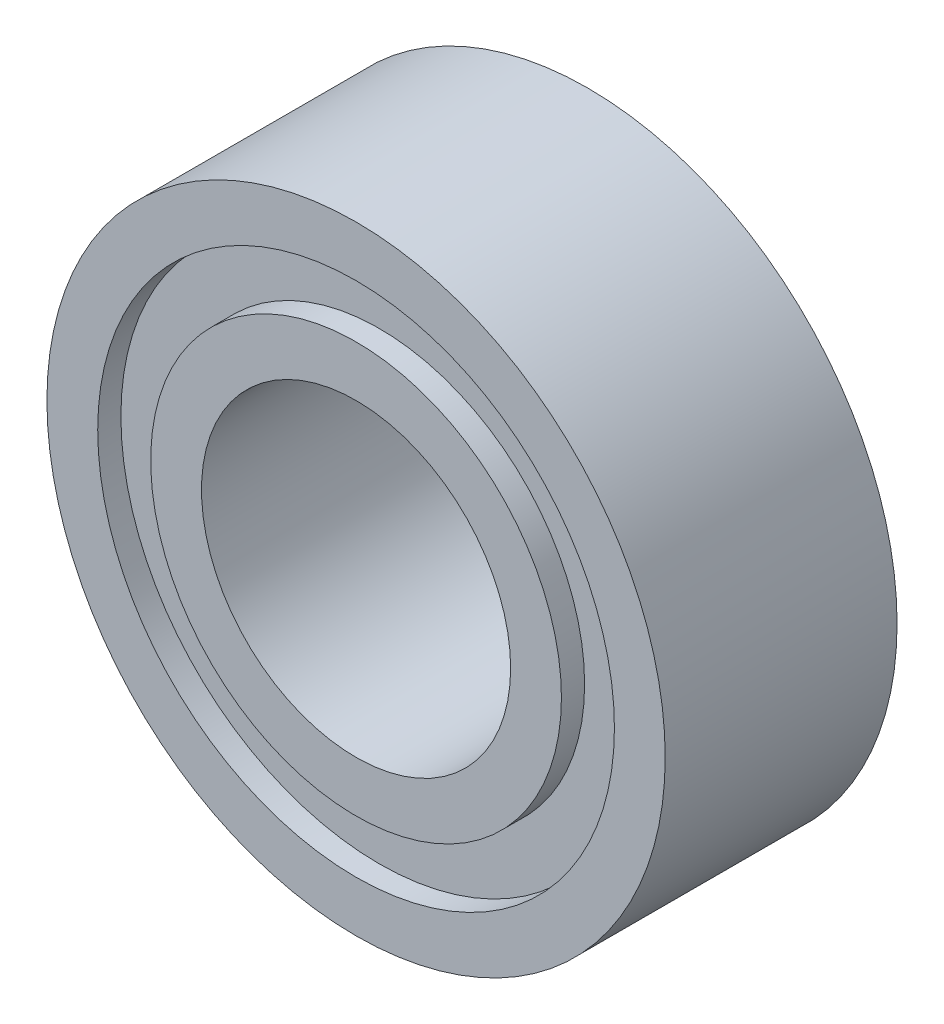
SolidWorks part; units mm, degrees
material "Легированная сталь"
ref_plane "Спереди" through (0, 0, 0) normal (0, 0, 1) x (1, 0, 0)
ref_plane "Сверху" through (0, 0, 0) normal (0, 1, 0) x (1, 0, 0)
ref_plane "Справа" through (0, 0, 0) normal (1, 0, 0) x (0, 0, -1)
sketch "Эскиз1" plane through (0, 0, 0) normal (1, 0, 0) x (0, 0, -1)
  line L0 (1.5, 2) -> (-1.5, 2)
  line L2 (-1.5, 4) -> (1.5, 4)
  line L4 (0, 0) -> (0, 50000) construction
  line L5 (-1.5, 2) -> (-1.5, 2.6571)
  line L6 (-1.5, 2.6571) -> (-1.2, 2.6571)
  line L7 (1.5, 2.6571) -> (1.5, 2)
  line L8 (-1.5, 4) -> (-1.5, 3.3429)
  line L9 (-1.5, 3.3429) -> (-1.2, 3.3429)
  line L10 (1.5, 3.3429) -> (1.5, 4)
  line L11 (0.4924, 3.3429) -> (1, 3.3429)
  line L12 (0.4924, 2.6571) -> (1, 2.6571)
  line L13 (-1, 3.3429) -> (-0.4924, 3.3429)
  line L15 (-1.2, 3.3429) -> (-1.2, 2.6571)
  line L17 (-1, 3.3429) -> (-1, 2.6571)
  line L18 (-1, 2.6571) -> (-0.4924, 2.6571)
  line L19 (1, 3.3429) -> (1, 2.6571)
  line L20 (1.2, 3.3429) -> (1.2, 2.6571)
  line L21 (1.2, 3.3429) -> (1.5, 3.3429)
  line L22 (1.2, 2.6571) -> (1.5, 2.6571)
  line L23 (0, 0) -> (50000, 0) construction
  arc A0 (-0.4924, 2.6571) -> (0.4924, 2.6571) centre (0, 3) ccw
  arc A1 (0.4924, 3.3429) -> (-0.4924, 3.3429) centre (0, 3) ccw
  dimension "D5" = 1.5
  dimension "D9" = 0.6
  dimension "D10" = 110.3
  dimension "D1" = 2
  dimension "D2" = 1.5
  dimension "D3" = 0.6571
  dimension "D4" = 4
  dimension "D6" = 1.5
  dimension "D7" = 1.5
  dimension "D8" = 3
  dimension "D11" = 1.2
  dimension "D12" = 0.2
revolve "Повернуть1" add sketch "Эскиз1" angle 360 about L23
